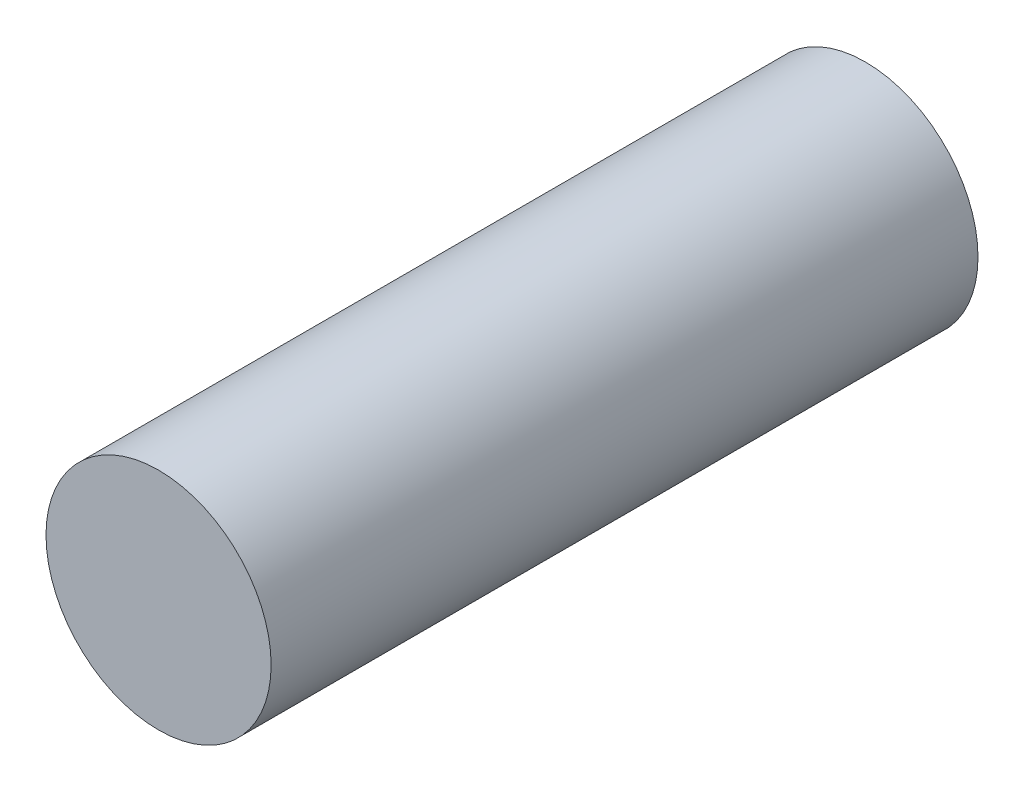
SolidWorks part; units mm, degrees
ref_plane "Front Plane" through (0, 0, 0) normal (0, 0, 1) x (1, 0, 0)
ref_plane "Top Plane" through (0, 0, 0) normal (0, 1, 0) x (1, 0, 0)
ref_plane "Right Plane" through (0, 0, 0) normal (1, 0, 0) x (0, 0, -1)
sketch "Sketch1" plane through (0, 0, 0) normal (0, 0, 1) x (1, 0, 0)
  circle A0 centre (0, 0) radius 500
  dimension "D1" = 1000
extrude "Boss-Extrude1" add sketch "Sketch1" along normal blind 3140
